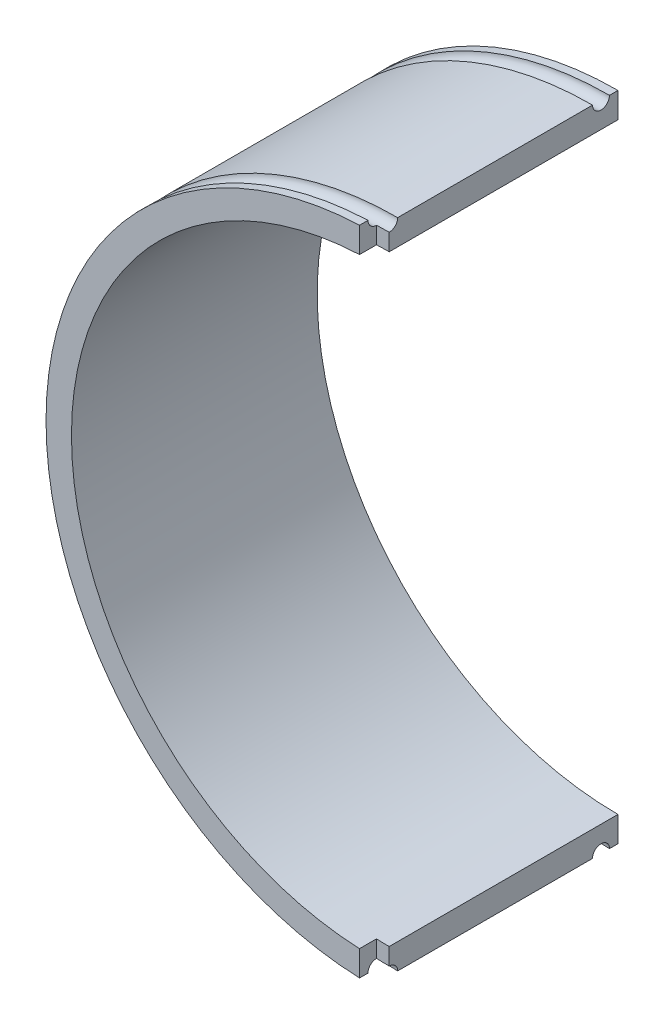
SolidWorks part; units mm, degrees
material "ABS"
ref_plane "Front Plane" through (0, 0, 0) normal (0, 0, 1) x (1, 0, 0)
ref_plane "Top Plane" through (0, 0, 0) normal (0, 1, 0) x (1, 0, 0)
ref_plane "Right Plane" through (0, 0, 0) normal (1, 0, 0) x (0, 0, -1)
sketch "Sketch1" plane through (0, 0, 0) normal (0, 0, 1) x (1, 0, 0)
  line L0 (0, 38.5) -> (0, 35.5)
  line L1 (0, -35.5) -> (0, -38.5)
  arc A0 (0, 35.5) -> (0, -35.5) centre (0, 0) ccw
  arc A1 (0, 38.5) -> (0, -38.5) centre (0, 0) ccw
  dimension "D1" = 3
  dimension "D2" = 77
extrude "Main Shell" add sketch "Sketch1" along normal blind 29
sketch "Sketch3" plane through (0, 0, 0) normal (1, 0, 0) x (0, 0, -1)
  line L0 (-29, 38.5) -> (0, 38.5) construction
  line L1 (-28, 38.5) -> (-26, 38.5)
  line L2 (-3, 38.5) -> (-1, 38.5)
  arc A0 (-28, 38.5) -> (-26, 38.5) centre (-27, 38.5) ccw
  arc A1 (-3, 38.5) -> (-1, 38.5) centre (-2, 38.5) ccw
  dimension "D1" = 2
  dimension "D2" = 2
  dimension "D3" = 2
revolve "Rubber Band Holder" cut sketch "Sketch3" angle 360 about axis through (0, 0, 29) along (0, 0, -1)
sketch "Sketch4" plane through (0, 0, 29) normal (0, 0, 1) x (1, 0, 0)
  line L0 (0, 38.5) -> (0, 35.5)
  line L1 (-1.5, 38.4708) -> (-1.5, 35.4683)
  line L2 (-1.5, -38.4708) -> (-1.5, -35.4683)
  line L3 (0, -38.5) -> (0, -35.5)
  line L4 (0, 0) -> (-38.5, 0) construction
  arc A0 (0, 35.5) -> (0, -35.5) centre (0, 0) ccw construction
  arc A1 (0, 35.5) -> (-1.5, 35.4683) centre (0, 0) ccw
  arc A2 (0, 38.5) -> (0, -38.5) centre (0, 0) ccw construction
  arc A3 (0, 38.5) -> (-1.5, 38.4708) centre (0, 0) ccw
  arc A4 (0, -38.5) -> (-1.5, -38.4708) centre (0, 0) cw
  arc A5 (0, -35.5) -> (-1.5, -35.4683) centre (0, 0) cw
  dimension "D1" = 1.5
extrude "End Stop" cut sketch "Sketch4" against normal blind 2
